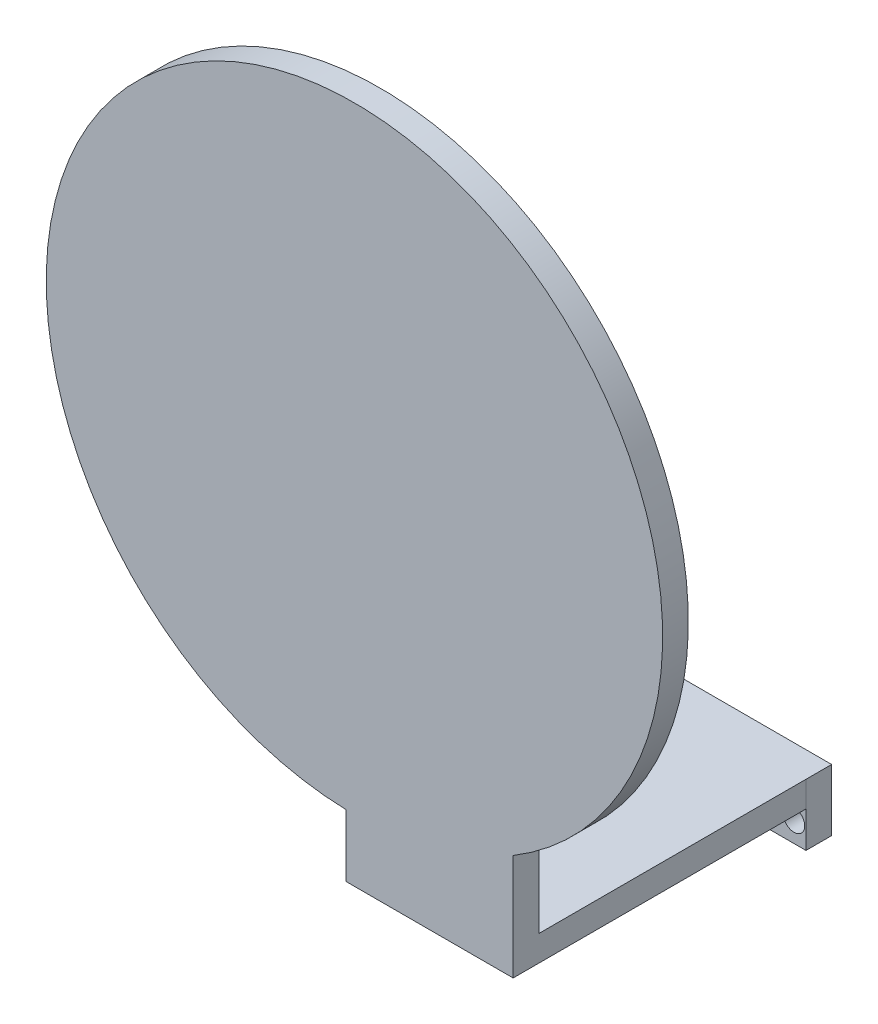
SolidWorks part; units mm, degrees
ref_plane "Front Plane" through (0, 0, 0) normal (0, 0, 1) x (1, 0, 0)
ref_plane "Top Plane" through (0, 0, 0) normal (0, 1, 0) x (1, 0, 0)
ref_plane "Right Plane" through (0, 0, 0) normal (1, 0, 0) x (0, 0, -1)
ref_plane "Plane1" through (0, 0, 0) normal (0, 0, 1) x (1, 0, 0)
sketch "Sketch2" plane through (0, 0, -25141.0647) normal (0, 0, 1) x (1, 0, 0)
  line L0 (344.2989, -3592.0657) -> (376.8389, -3592.0657)
  line L1 (344.2989, -3592.0657) -> (344.2989, -3600.0657)
  line L2 (376.8389, -3592.0657) -> (376.8389, -3600.0657)
  line L3 (344.2989, -3600.0657) -> (376.8389, -3600.0657)
  circle A0 centre (374.5011, -3596.0608) radius 2.1
  circle A1 centre (358.0135, -3596.0608) radius 2.1 construction
  circle A5 centre (374.5011, -3596.0608) radius 2.1 construction
  circle A6 centre (358.0135, -3596.0608) radius 2.1
  dimension "D2" = 32.54
  dimension "D7" = 4.2
  dimension "D9" = 4.2
  dimension "D1" = 8
  dimension "D3" = 13.7146
  dimension "D10" = 4.0049
extrude "Boss-Extrude1" add sketch "Sketch2" along normal blind 5
sketch "Sketch3" plane through (0, -3592.0657, 0) normal (0, 1, 0) x (1, 0, 0)
  line L0 (376.8389, 25136.0647) -> (344.2989, 25136.0647)
  line L1 (376.8389, 25136.0647) -> (376.8389, 25141.0647)
  line L2 (344.2989, 25136.0647) -> (344.2989, 25141.0647)
  line L3 (376.8389, 25141.0647) -> (344.2989, 25141.0647)
extrude "Boss-Extrude2" add sketch "Sketch3" along normal blind 4
sketch "Sketch4" plane through (0, 0, -25136.0647) normal (0, 0, 1) x (1, 0, 0)
  line L0 (376.8386, -3588.0657) -> (344.2989, -3588.0657)
  line L1 (376.8386, -3588.0657) -> (376.8386, -3593.0657)
  line L2 (344.2989, -3588.0657) -> (344.2989, -3593.0657)
  line L3 (376.8386, -3593.0657) -> (344.2989, -3593.0657)
  line L6 (344.2989, -3588.0657) -> (344.2989, -3600.0657) construction
  line L7 (344.2989, -3588.0657) -> (376.8389, -3588.0657) construction
  dimension "D1" = 5
extrude "Boss-Extrude3" add sketch "Sketch4" along normal blind 57
sketch "Sketch5" plane through (0, -3588.0657, 0) normal (0, 1, 0) x (1, 0, 0)
  line L0 (376.8386, 25079.0647) -> (344.2989, 25079.0647)
  line L1 (376.8386, 25079.0647) -> (376.8386, 25084.0647)
  line L2 (344.2989, 25079.0647) -> (344.2989, 25084.0647)
  line L3 (376.8386, 25084.0647) -> (344.2989, 25084.0647)
  line L5 (376.8386, 25079.0647) -> (376.8386, 25136.0647) construction
  line L6 (344.2989, 25079.0647) -> (344.2989, 25136.0647) construction
  line L7 (376.8386, 25079.0647) -> (344.2989, 25079.0647) construction
  dimension "D1" = 5
extrude "Boss-Extrude4" add sketch "Sketch5" along normal blind 27.5
sketch "Sketch7" plane through (0, 0, -25079.0647) normal (0, 0, 1) x (1, 0, 0)
  circle A0 centre (345.9463, -3520.9722) radius 60
  circle A1 centre (345.9463, -3520.9722) radius 62.5 construction
  dimension "D1" = 120
extrude "Boss-Extrude6" add sketch "Sketch7" against normal blind 5
